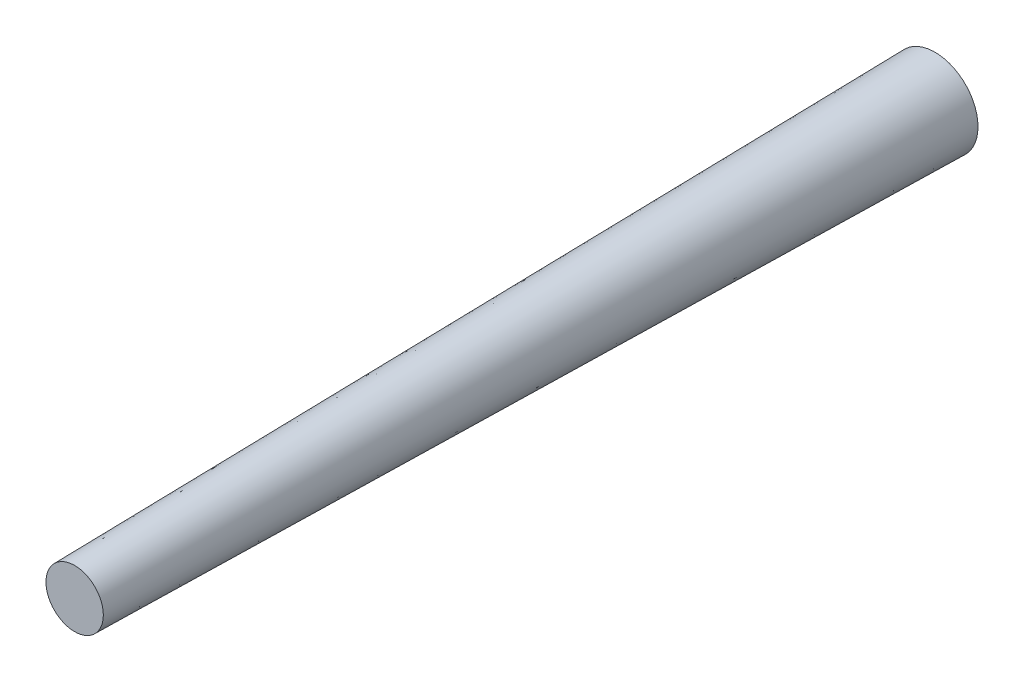
SolidWorks part; units mm, degrees
ref_plane "Front Plane" through (0, 0, 0) normal (0, 0, 1) x (1, 0, 0)
ref_plane "Top Plane" through (0, 0, 0) normal (0, 1, 0) x (1, 0, 0)
ref_plane "Right Plane" through (0, 0, 0) normal (1, 0, 0) x (0, 0, -1)
sketch "Sketch1" plane through (0, 0, 0) normal (0, 0, 1) x (1, 0, 0)
  circle A0 centre (0, 0) radius 3
  dimension "D1" = 6
extrude "Boss-Extrude1" add sketch "Sketch1" along normal blind 60 draft 0.954
